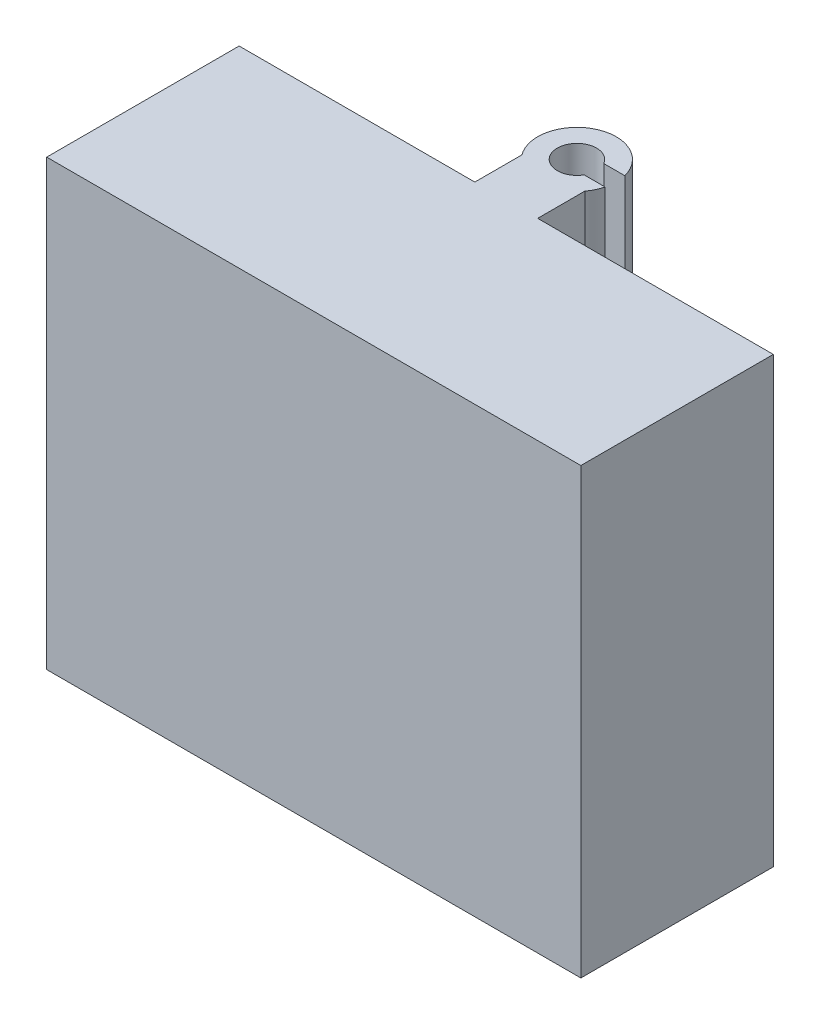
SolidWorks part; units mm, degrees
ref_plane "前视基准面" through (0, 0, 0) normal (0, 0, 1) x (1, 0, 0)
ref_plane "上视基准面" through (0, 0, 0) normal (0, 1, 0) x (1, 0, 0)
ref_plane "右视基准面" through (0, 0, 0) normal (1, 0, 0) x (0, 0, -1)
sketch "草图1" plane through (0, 0, 0) normal (0, 0, 1) x (1, 0, 0)
  line L0 (0, 0) -> (68, 0)
  line L1 (68, 0) -> (68, -56.5)
  line L2 (68, -56.5) -> (0, -56.5)
  line L3 (0, -56.5) -> (0, 0)
extrude "凸台-拉伸1" add sketch "草图1" along normal blind 24.5
sketch "草图4" plane through (0, -56.5, 0) normal (0, -1, 0) x (1, 0, 0)
  line L1 (1.45, 23) -> (1.45, 1.5)
  line L2 (66.55, 23) -> (66.55, 1.5)
  line L3 (66.55, 23) -> (1.45, 23)
  line L5 (1.45, 1.5) -> (66.55, 1.5)
extrude "切除-拉伸2" cut sketch "草图4" against normal blind 55
sketch "草图6" plane through (0, 0, 0) normal (0, 0, -1) x (-1, 0, 0)
  line L0 (-38, 0) -> (-30, 0)
  line L2 (0, -56.5) -> (-68, -56.5) construction
  line L8 (-30, -56.5) -> (-38, -56.5)
  line L9 (-38, 0) -> (-38, -56.5)
  line L10 (-30, 0) -> (-30, -56.5)
extrude "凸台-拉伸3" add sketch "草图6" along normal blind 6
sketch "草图8" plane through (0, 0, 0) normal (0, 1, 0) x (1, 0, 0)
  line L0 (38, 6) -> (34, 6)
  line L1 (30, 6) -> (38, 6) construction
  line L3 (36.1651, 7.75) -> (36.1651, 10.25)
  line L6 (36.1651, 7.75) -> (38.8412, 7.75)
  line L8 (36.1651, 10.25) -> (38.8412, 10.25)
  arc A0 (38, 6) -> (30, 6) centre (34, 9) ccw
  circle A1 centre (34, 9) radius 2.5
  line M4 (38, 6) -> (30, 6)
extrude "凸台-拉伸4" add sketch "草图8" against normal blind 56.5 contours A1 L8 A0 L6 M4
sketch "草图9" plane through (0, 0, 0) normal (0, 0, -1) x (-1, 0, 0)
  line L0 (-24.397, -56.5) -> (-43.397, -56.5)
  line L1 (0, -56.5) -> (-30, -56.5) construction
  line L2 (-38, -56.5) -> (-68, -56.5) construction
  line L3 (-43.397, -56.5) -> (-43.397, -23.5)
  line L4 (-43.397, -23.5) -> (-24.397, -23.5)
  line L5 (-24.397, -23.5) -> (-24.397, -56.5)
extrude "切除-拉伸3" cut sketch "草图9" along normal blind 15
